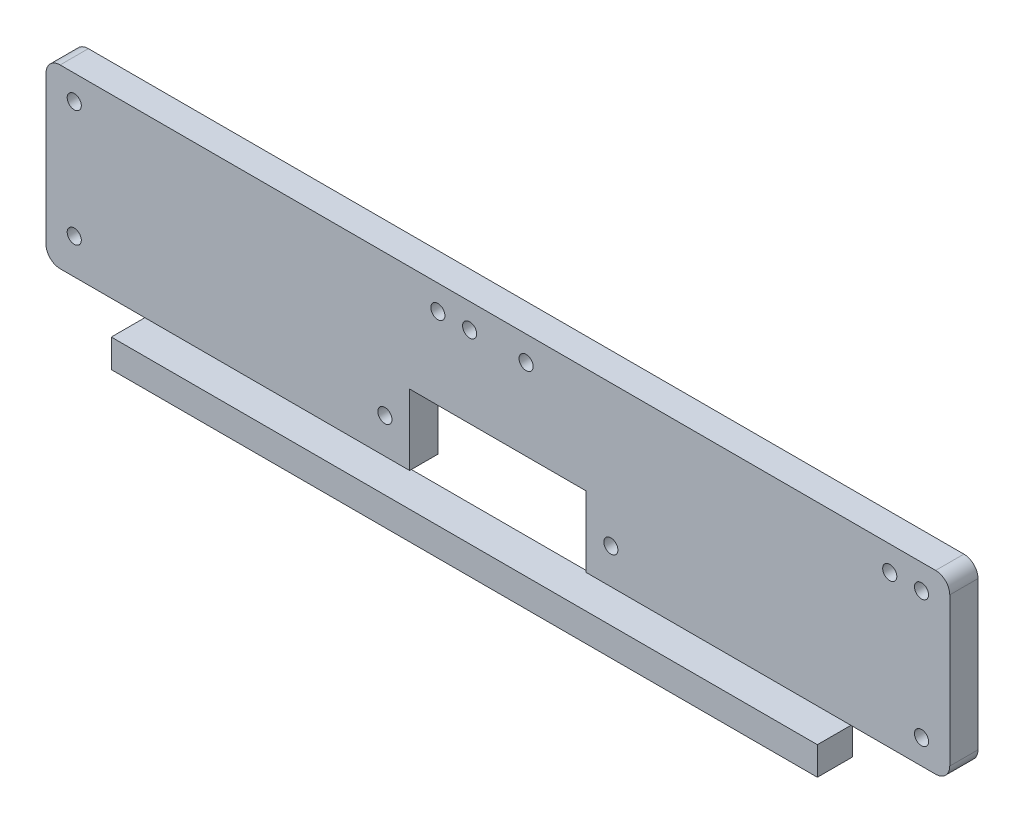
SolidWorks part; units mm, degrees
material "ABS"
ref_plane "Front Plane" through (0, 0, 0) normal (0, 0, 1) x (1, 0, 0)
ref_plane "Top Plane" through (0, 0, 0) normal (0, 1, 0) x (1, 0, 0)
ref_plane "Right Plane" through (0, 0, 0) normal (1, 0, 0) x (0, 0, -1)
sketch "Sketch1" plane through (0, 0, 0) normal (0, 0, 1) x (1, 0, 0)
  line L1 (-127.7162, 72.1061) -> (128.2838, 72.1061)
  line L2 (-127.7162, 72.1061) -> (-127.7162, 22.1061)
  line L3 (-127.7162, 22.1061) -> (128.2838, 22.1061)
  line L4 (128.2838, 72.1061) -> (128.2838, 22.1061)
  circle A1 centre (120.2838, 65.1061) radius 2
  circle A2 centre (111.2838, 65.1061) radius 2
  circle A3 centre (8.2838, 65.1061) radius 2
  circle A4 centre (-7.7162, 65.1061) radius 2
  circle A5 centre (-16.7162, 65.1061) radius 2
  circle A6 centre (-119.7162, 65.1061) radius 2
  dimension "D3" = 4
  dimension "D1" = 256
  dimension "D2" = 50
  dimension "D4" = 7
  dimension "D5" = 9
  dimension "D6" = 8
  dimension "D7" = 103
  dimension "D8" = 16
  dimension "D9" = 9
  dimension "D10" = 103
extrude "Boss-Extrude1" add sketch "Sketch1" along normal blind 8
fillet "Fillet1" radius 4 4 edges at (-127.7162, 22.1061, 4) (128.2838, 22.1061, 4) (128.2838, 72.1061, 4) (-127.7162, 72.1061, 4)
sketch "Sketch2" plane through (0, 0, 8) normal (0, 0, 1) x (1, 0, 0)
  line L0 (-123.7162, 22.1061) -> (124.2838, 22.1061) construction
  line L1 (-24.7162, 34.1061) -> (25.2838, 34.1061)
  line L2 (-24.7162, 34.1061) -> (-24.7162, 22.1061)
  line L3 (-24.7162, 22.1061) -> (25.2838, 22.1061)
  line L4 (25.2838, 34.1061) -> (25.2838, 22.1061)
  line L5 (-127.7162, 68.1061) -> (-127.7162, 26.1061) construction
  line L7 (-32.7162, 22.1061) -> (-39.7162, 22.1061)
  line L8 (-32.7162, 22.1061) -> (-32.7162, 14.1061)
  line L9 (-32.7162, 14.1061) -> (-39.7162, 14.1061)
  line L10 (-39.7162, 22.1061) -> (-39.7162, 14.1061)
  line L11 (33.2838, 22.1061) -> (40.2838, 22.1061)
  line L12 (33.2838, 22.1061) -> (33.2838, 14.1061)
  line L13 (33.2838, 14.1061) -> (40.2838, 14.1061)
  line L14 (40.2838, 22.1061) -> (40.2838, 14.1061)
  line M18 (-123.7162, 22.1061) -> (124.2838, 22.1061)
  dimension "D1" = 50
  dimension "D2" = 12
  dimension "D3" = 103
  dimension "D4" = 7
  dimension "D5" = 8
  dimension "D6" = 8
  dimension "D7" = 8
extrude "Boss-Extrude2" add sketch "Sketch2" against normal blind 8 contours L14 L12 L13 M18 | L8 L7 L10 L9
sketch "Sketch3" plane through (0, 0, 8) normal (0, 0, 1) x (1, 0, 0)
  line L0 (-32.7162, 22.1061) -> (33.2838, 22.1061) construction
  line L1 (-24.7162, 42.1061) -> (25.2838, 42.1061)
  line L2 (-24.7162, 42.1061) -> (-24.7162, 22.1061)
  line L3 (-24.7162, 22.1061) -> (25.2838, 22.1061)
  line L4 (25.2838, 42.1061) -> (25.2838, 22.1061)
  line L5 (-32.7162, 22.1061) -> (-32.7162, 14.1061) construction
  dimension "D1" = 50
  dimension "D2" = 8
  dimension "D3" = 20
extrude "Cut-Extrude1" cut sketch "Sketch3" against normal blind 8
sketch "Sketch4" plane through (0, 0, 8) normal (0, 0, 1) x (1, 0, 0)
  line L0 (-32.7162, 22.1061) -> (-24.7162, 22.1061) construction
  line L1 (-24.7162, 42.1061) -> (-24.7162, 22.1061) construction
  line L2 (25.2838, 22.1061) -> (25.2838, 42.1061) construction
  line L3 (25.2838, 22.1061) -> (33.2838, 22.1061) construction
  line L4 (40.2838, 22.1061) -> (124.2838, 22.1061) construction
  line L5 (128.2838, 26.1061) -> (128.2838, 68.1061) construction
  line L6 (-123.7162, 22.1061) -> (-39.7162, 22.1061) construction
  line L7 (-127.7162, 68.1061) -> (-127.7162, 26.1061) construction
  circle A0 centre (-31.7162, 32.1061) radius 2
  circle A1 centre (32.2838, 32.1061) radius 2
  circle A2 centre (-119.7162, 32.1061) radius 2
  circle A3 centre (120.2838, 29.1061) radius 2
  dimension "D1" = 4
  dimension "D2" = 10
  dimension "D3" = 7
  dimension "D4" = 7
  dimension "D5" = 10
  dimension "D6" = 7
  dimension "D7" = 8
  dimension "D8" = 10
  dimension "D9" = 8
extrude "Cut-Extrude2" cut sketch "Sketch4" against normal blind 8
sketch "Sketch5" plane through (-39.7162, 0, 0) normal (-1, 0, 0) x (0, 0, 1)
  line L0 (0, 22.1061) -> (0, 14.1061) construction
  line L1 (0, 14.1061) -> (8, 14.1061) construction
  circle A0 centre (3.5, 18.1061) radius 1.75
  dimension "D2" = 3.5
  dimension "D1" = 3.5
  dimension "D3" = 4
extrude "Cut-Extrude3" cut sketch "Sketch5" against normal blind 113
sketch "Sketch8" plane through (0, 0, 0) normal (0, 0, 1) x (1, 0, 0)
  line L0 (-32.7162, 22.1061) -> (33.2838, 22.1061) construction
  line L1 (-32.7162, 14.1061) -> (33.2838, 14.1061) construction
  line L2 (0.2838, 22.1061) -> (0.2838, 14.1061) construction
  line L4 (-99.7162, 22.1061) -> (100.2838, 22.1061)
  line L5 (-99.7162, 22.1061) -> (-99.7162, 14.1061)
  line L6 (-99.7162, 14.1061) -> (100.2838, 14.1061)
  line L7 (100.2838, 22.1061) -> (100.2838, 14.1061)
  line L8 (-99.7162, 22.1061) -> (100.2838, 14.1061) construction
  line L9 (-99.7162, 14.1061) -> (100.2838, 22.1061) construction
  point P10 (0.2838, 18.1061)
  dimension "D1" = 200
  dimension "D2" = 8
extrude "Boss-Extrude12" add sketch "Sketch8" along normal blind 10 from offset 7.5
